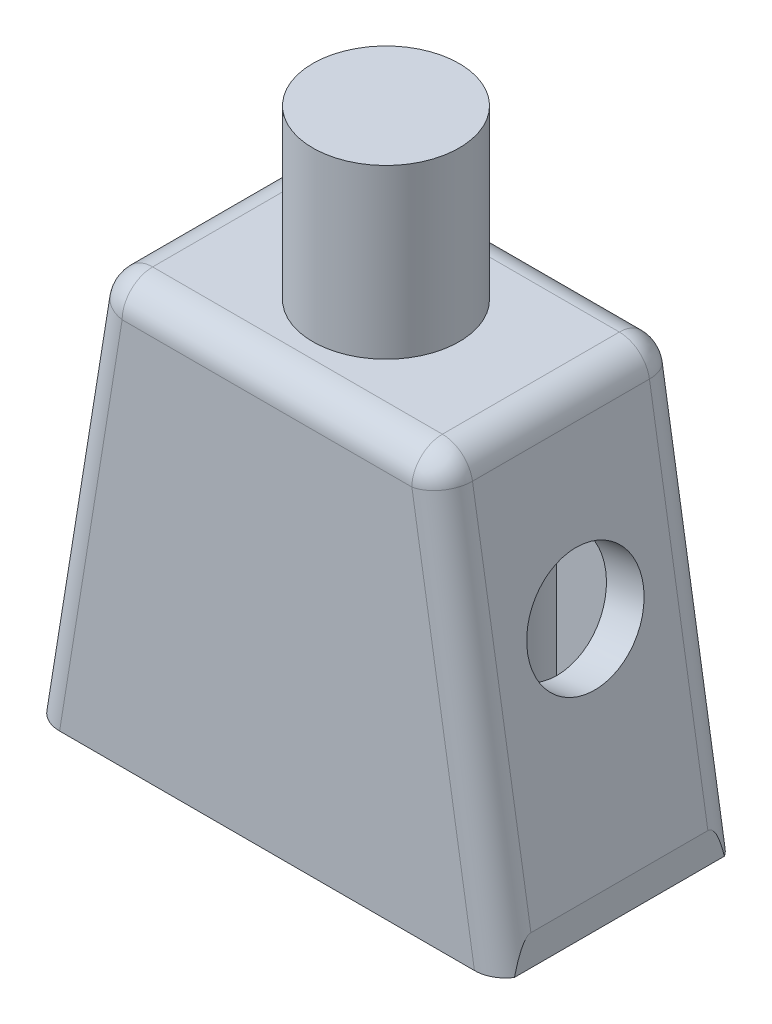
SolidWorks part; units mm, degrees
ref_plane "Front Plane" through (0, 0, 0) normal (0, 0, 1) x (1, 0, 0)
ref_plane "Top Plane" through (0, 0, 0) normal (0, 1, 0) x (1, 0, 0)
ref_plane "Right Plane" through (0, 0, 0) normal (1, 0, 0) x (0, 0, -1)
sketch "Sketch1" plane through (0, 0, 0) normal (0, 0, 1) x (1, 0, 0)
  line L0 (-7.65, -5.85) -> (-7.65, -6.85)
  line L1 (-7.65, -6.85) -> (7.65, -6.85)
  line L2 (7.65, -6.85) -> (7.65, -5.85)
  line L3 (7.65, -5.85) -> (5.5999, 6.85)
  line L4 (5.5999, 6.85) -> (-5.6001, 6.85)
  line L5 (-5.6001, 6.85) -> (-7.65, -5.85)
  dimension "D1" = 15.3
  dimension "D2" = 1
  dimension "D3" = 1
  dimension "D4" = 11.2
  dimension "D5" = 12.7
  dimension "D6" = 80.83
  dimension "D7" = 6.85
  dimension "D8" = 7.65
extrude "Boss-Extrude1" add sketch "Sketch1" along normal mid plane 7.8
shell "Shell5" thickness 1.25
sketch "Sketch2" plane through (0, 6.85, 0) normal (0, 1, 0) x (1, 0, 0)
  circle A0 centre (0, 0) radius 2.4
  dimension "D1" = 4.8
extrude "Boss-Extrude2" add sketch "Sketch2" along normal blind 5.5
sketch "Sketch5" plane through (0, 5.6, 0) normal (0, -1, 0) x (1, 0, 0)
  line L0 (-1.5, 1.25) -> (-1.5, 2.65)
  line L1 (4.5355, 2.65) -> (-4.5357, 2.65) construction
  line L2 (-1.5, 2.65) -> (1.5308, 2.65)
  line L3 (1.5308, 2.65) -> (1.5308, 1.25)
  line L4 (-1.5, -1.25) -> (-1.5, -2.65)
  line L5 (4.5355, -2.65) -> (-4.5357, -2.65) construction
  line L6 (-1.5, -2.65) -> (1.5308, -2.65)
  line L7 (1.5308, -2.65) -> (1.5308, -1.25)
  line L8 (-2.9, -2.65) -> (-1.5, -2.65)
  line L10 (2.9308, -2.65) -> (1.5308, -2.65)
  line L12 (2.9308, 2.65) -> (1.5308, 2.65)
  line L14 (-1.5, 2.65) -> (-2.9, 2.65)
  arc A0 (-2.9, -2.65) -> (-1.5, -1.25) centre (-1.5, -2.65) cw
  arc A1 (1.5308, -1.25) -> (2.9308, -2.65) centre (1.5308, -2.65) cw
  arc A2 (-1.5, 1.25) -> (-2.9, 2.65) centre (-1.5, 2.65) cw
  arc A3 (1.5308, 1.25) -> (2.9308, 2.65) centre (1.5308, 2.65) ccw
  dimension "D3" = 1.4
  dimension "D4" = 1.4
  dimension "D5" = 1.4
  dimension "D6" = 1.4
  dimension "D1" = 1.5
  dimension "D2" = 1.5308
extrude "Boss-Extrude3" add sketch "Sketch5" along normal through all contours L4 A0 L8 | L7 A1 L10 | L3 A3 L12 | L0 A2 L14
sketch "Sketch6" plane through (0, 5.6, 0) normal (0, -1, 0) x (1, 0, 0)
  circle A0 centre (0, 0) radius 0.7
  dimension "D1" = 1.4
extrude "Cut-Extrude2" cut sketch "Sketch6" against normal blind 4.25
sketch "Sketch7" plane through (6.5353, 1.055, 0) normal (0.9872, 0.1594, 0) x (0, 0, -1)
  circle A0 centre (0, 0) radius 1.9
  dimension "D1" = 3.8
extrude "Cut-Extrude3" cut sketch "Sketch7" against normal up to next
sketch "Sketch8" plane through (-6.5355, 1.0549, 0) normal (-0.9872, 0.1593, 0) x (0, 0, 1)
  circle A0 centre (0, 0) radius 1.9
  dimension "D1" = 3.8
extrude "Cut-Extrude4" cut sketch "Sketch8" against normal up to next
fillet "Fillet1" radius 1 8 edges at (-6.6251, 0.5, -3.9) (6.6249, 0.5, -3.9) (-0.0001, 6.85, -3.9) (-5.6001, 6.85, 0) (-6.6251, 0.5, 3.9) (-0.0001, 6.85, 3.9) (6.6249, 0.5, 3.9) (5.5999, 6.85, 0)
